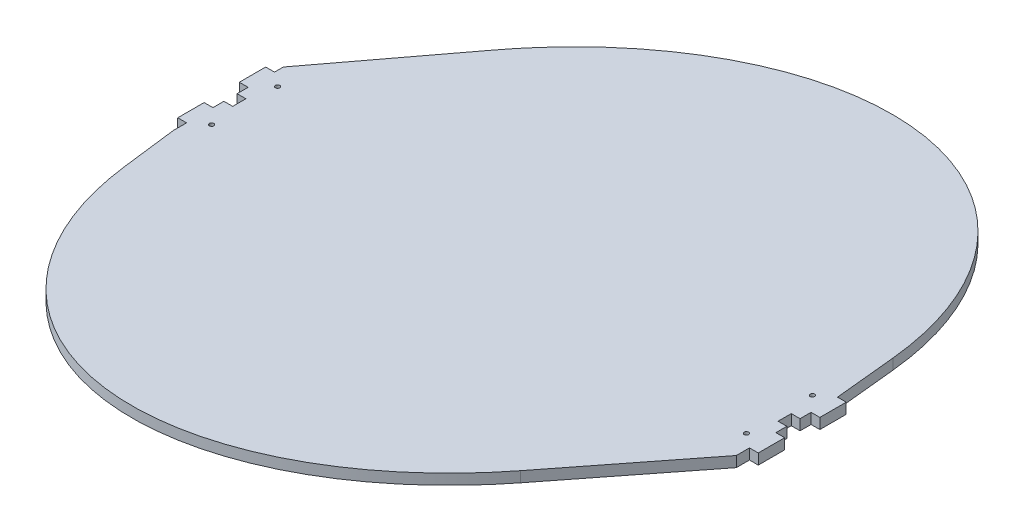
SolidWorks part; units mm, degrees
ref_plane "Front Plane" through (0, 0, 0) normal (0, 0, 1) x (1, 0, 0)
ref_plane "Top Plane" through (0, 0, 0) normal (0, 1, 0) x (1, 0, 0)
ref_plane "Right Plane" through (0, 0, 0) normal (1, 0, 0) x (0, 0, -1)
sketch "Sketch1" plane through (0, 0, 0) normal (0, 1, 0) x (1, 0, 0)
  line L0 (-320, -65) -> (-312.1702, -128.3352)
  line L1 (-217.5479, 195.7385) -> (-320, 60)
  line L2 (-320, 60) -> (-320, 50)
  line L3 (-320, 50) -> (-330, 50)
  line L4 (-330, 50) -> (-330, 20)
  line L5 (-330, 20) -> (-320, 20)
  line L6 (-320, 20) -> (-320, -20)
  line L7 (-320, -20) -> (-330, -20)
  line L8 (-330, -20) -> (-330, -50)
  line L9 (-330, -50) -> (-320, -50)
  line L10 (-320, -50) -> (-320, -65)
  line L11 (212.2821, -202.5885) -> (320, -65)
  line L12 (320, -50) -> (320, -65)
  line L13 (320, -50) -> (330, -50)
  line L14 (330, -50) -> (330, -20)
  line L15 (330, -20) -> (320, -20)
  line L16 (320, -20) -> (320, 20)
  line L17 (320, 20) -> (330, 20)
  line L18 (330, 20) -> (330, 50)
  line L19 (330, 50) -> (320, 50)
  line L20 (320, 50) -> (320, 51)
  line L21 (320, 51) -> (313.0913, 120.0927)
  ellipse E0 centre (0, 0) end of major axis (-190, -329.0897) minor radius 290 (313.0913, 120.0927) -> (-217.5479, 195.7385) ccw
  ellipse E1 centre (0, 0) end of major axis (-190, -329.0897) minor radius 290 (-312.1702, -128.3352) -> (212.2821, -202.5885) ccw
extrude "Boss-Extrude1" add sketch "Sketch1" along normal blind 12
sketch "Sketch2" plane through (0, 0, 0) normal (0, -1, 0) x (1, 0, 0)
  line L0 (0, 0) -> (595.7693, 0) construction
  line L1 (320, 20) -> (320, -20) construction
  line L2 (320, -7.5) -> (310, -7.5)
  line L3 (320, -7.5) -> (320, 7.5)
  line L4 (320, 7.5) -> (310, 7.5)
  line L5 (310, -7.5) -> (310, 7.5)
  line L6 (0, 0) -> (0, 484.7158) construction
  line L7 (-310, -7.5) -> (-310, 7.5)
  line L8 (-320, 7.5) -> (-310, 7.5)
  line L9 (-320, -7.5) -> (-320, 7.5)
  line L10 (-320, -7.5) -> (-310, -7.5)
  point P3 (-320, 0)
  point P10 (310, 0)
  point P11 (320, 0)
  point P13 (-310, 0)
  dimension "D1" = 15
  dimension "D2" = 10
extrude "Cut-Extrude1" cut sketch "Sketch2" against normal blind 12
hole_wizard "Ø5.0 (5) Diameter Hole2" positions "Sketch5" profile "Sketch6" hole size "Ø5.0" standard "ANSI Metric"
sketch "Sketch5" plane through (0, -12, 0) normal (0, -1, 0) x (-1, 0, 0)
  point P0 (304, 37.5)
  point P3 (304, -37.5)
  point P6 (-304, -37.5)
  point P9 (-304, 37.5)
sketch "Sketch6" plane through (-304, -12, -37.5) normal (1, 0, 0) x (0, 0, -1)
  line L0 (0, 0) -> (0, 26.5022)
  line L1 (0, 26.5022) -> (2.5, 25)
  line L2 (2.5, 25) -> (2.5, 0)
  line L3 (2.5, 0) -> (0, 0)
  line L4 (0, 26.5022) -> (-2.5, 25) construction
  line L5 (0, -6.35) -> (0, 107.95) construction
  dimension "Hole Dia." = 5
  dimension "Hole Depth" = 25
  dimension "Drill Angle" = 118
